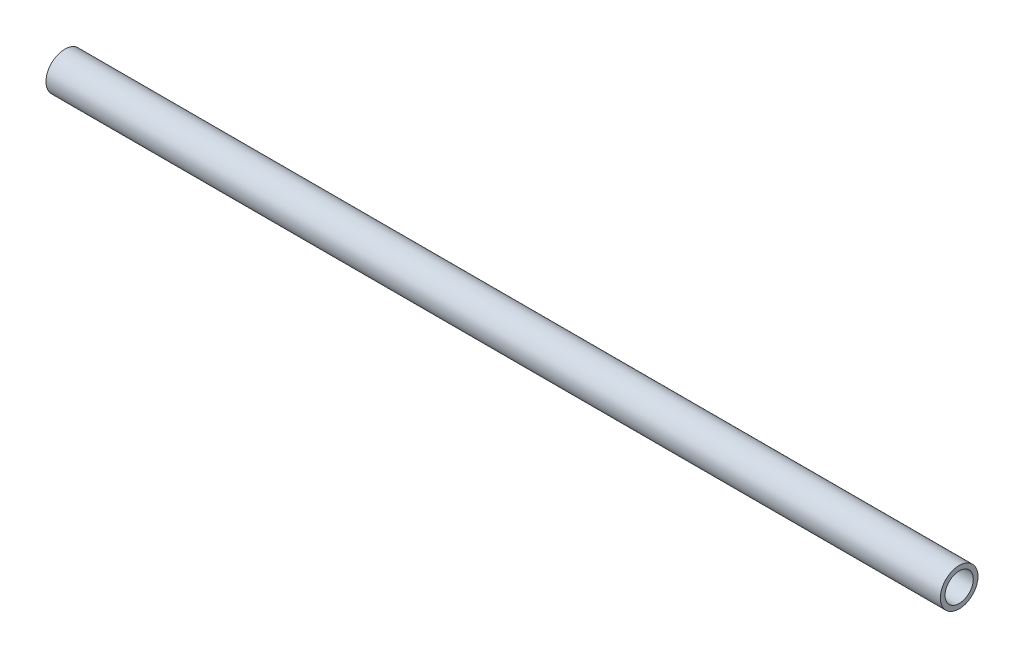
SolidWorks part; units mm, degrees
material "Thornel Mat VMA"
ref_plane "Front" through (0, 0, 0) normal (0, 0, 1) x (1, 0, 0)
ref_plane "Top" through (0, 0, 0) normal (0, 1, 0) x (1, 0, 0)
ref_plane "Right" through (0, 0, 0) normal (1, 0, 0) x (0, 0, -1)
sketch "Sketch1" plane through (0, 0, 0) normal (1, 0, 0) x (0, 0, -1)
  circle A0 centre (0, 0) radius 4
  circle A1 centre (0, 0) radius 3
  dimension "D1" = 8
  dimension "D2" = 6
extrude "Boss-Extrude1" add sketch "Sketch1" along normal mid plane 190
